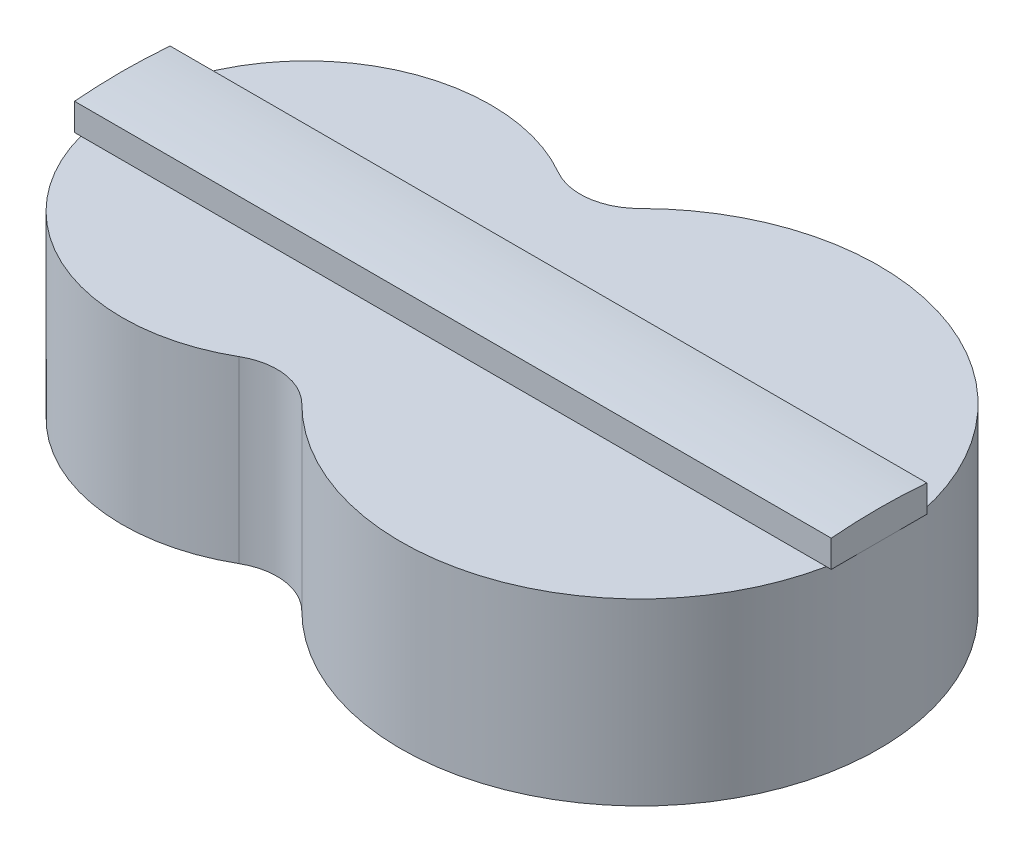
SolidWorks part; units mm, degrees
ref_plane "Front Plane" through (0, 0, 0) normal (0, 0, 1) x (1, 0, 0)
ref_plane "Top Plane" through (0, 0, 0) normal (0, 1, 0) x (1, 0, 0)
ref_plane "Right Plane" through (0, 0, 0) normal (1, 0, 0) x (0, 0, -1)
sketch "Sketch1" plane through (0, 0, 0) normal (0, 1, 0) x (1, 0, 0)
  line L0 (100, 0) -> (-500, 0) construction
  arc A0 (-70.7107, -70.7107) -> (-70.7107, 70.7107) centre (0, 0) ccw
  arc A1 (-70.7107, 70.7107) -> (-100.8883, 66.7377) centre (-88.3883, 88.3883) cw
  arc A3 (-100.8883, 66.7377) -> (-100.8883, -66.7377) centre (-139.4194, 0) ccw
  arc A4 (-70.7107, -70.7107) -> (-100.8883, -66.7377) centre (-88.3883, -88.3883) ccw
extrude "Boss-Extrude3" add sketch "Sketch1" against normal blind 75
sketch "Sketch4" plane through (0, 0, 0) normal (0, 1, 0) x (1, 0, 0)
  line L0 (-235.662, 0) -> (0, 0) construction
  line L1 (-66.1438, 75) -> (64.2836, 76.6004) construction
  line L2 (-66.1438, 0) -> (-66.1438, 75) construction
  arc A0 (-70.7107, -70.7107) -> (-70.7107, 70.7107) centre (0, 0) ccw construction
sketch "Sketch6" plane through (0, 0, 0) normal (1, 0, 0) x (0, 0, -1)
  line L0 (0, 195.3917) -> (0, 0) construction
  line L1 (0, 0) -> (0, -458.9045) construction
  line L2 (20, 0) -> (20, 11.3262)
  line L3 (0, 0) -> (75, 0) construction
  line L4 (-100, -75) -> (100, -75) construction
  line L5 (20, 0) -> (-20, 0)
  line L6 (-20, 0) -> (-20, 11.3262)
  arc A0 (20, 11.3262) -> (-20, 11.3262) centre (0, -225) ccw
  dimension "D2" = 150
  dimension "D3" = 237.171
  dimension "D1" = 20
extrude "Boss-Extrude4" add sketch "Sketch6" along normal through all and the other way through all contours A0 L6 L5 L2
sketch "Sketch7" plane through (0, -75, 0) normal (0, -1, 0) x (1, 0, 0)
  line L0 (-216.4815, 0) -> (100, 0) construction
  line L1 (-66.1438, 0) -> (-66.1438, -75) construction
  arc A0 (-70.7107, -70.7107) -> (-70.7107, 70.7107) centre (0, 0) ccw construction
